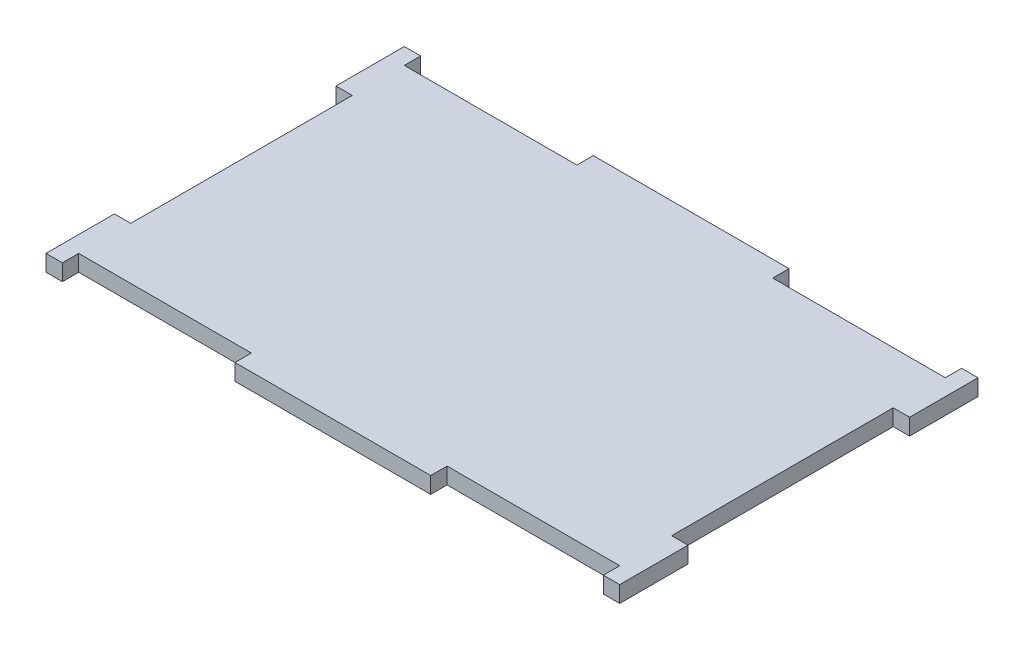
SolidWorks part; units mm, degrees
ref_plane "Front Plane" through (0, 0, 0) normal (0, 0, 1) x (1, 0, 0)
ref_plane "Top Plane" through (0, 0, 0) normal (0, 1, 0) x (1, 0, 0)
ref_plane "Right Plane" through (0, 0, 0) normal (1, 0, 0) x (0, 0, -1)
sketch "Sketch1" plane through (0, 0, 0) normal (0, 1, 0) x (1, 0, 0)
  line L0 (0, 34.775) -> (111.35, 34.775) construction
  line L1 (0, 0) -> (111.35, 0)
  line L2 (0, 0) -> (0, 69.55)
  line L3 (0, 69.55) -> (111.35, 69.55)
  line L4 (111.35, 0) -> (111.35, 69.55)
  line L5 (55.675, 69.55) -> (55.675, 0) construction
  line L6 (108.175, 56.275) -> (111.35, 13.275) construction
  line L7 (3.175, 13.275) -> (0, 13.275)
  line L8 (3.175, 13.275) -> (3.175, 56.275)
  line L9 (3.175, 56.275) -> (0, 56.275)
  line L10 (0, 13.275) -> (0, 56.275)
  line L11 (3.175, 13.275) -> (0, 56.275) construction
  line L12 (3.175, 56.275) -> (0, 13.275) construction
  line L13 (74.675, 66.375) -> (36.675, 66.375)
  line L14 (74.675, 66.375) -> (74.675, 69.55)
  line L15 (74.675, 69.55) -> (36.675, 69.55)
  line L16 (36.675, 66.375) -> (36.675, 69.55)
  line L17 (74.675, 66.375) -> (36.675, 69.55) construction
  line L18 (74.675, 69.55) -> (36.675, 66.375) construction
  line L19 (3.175, 66.375) -> (36.675, 66.375)
  line L20 (3.175, 66.375) -> (3.175, 69.55)
  line L21 (3.175, 69.55) -> (36.675, 69.55)
  line L22 (36.675, 66.375) -> (36.675, 69.55)
  line L23 (3.175, 66.375) -> (36.675, 69.55) construction
  line L24 (3.175, 69.55) -> (36.675, 66.375) construction
  line L25 (108.175, 66.375) -> (74.675, 66.375)
  line L26 (108.175, 66.375) -> (108.175, 69.55)
  line L27 (108.175, 69.55) -> (74.675, 69.55)
  line L28 (74.675, 66.375) -> (74.675, 69.55)
  line L29 (108.175, 66.375) -> (74.675, 69.55) construction
  line L30 (108.175, 69.55) -> (74.675, 66.375) construction
  line L31 (108.175, 13.275) -> (111.35, 56.275) construction
  line L32 (111.35, 13.275) -> (111.35, 56.275)
  line L33 (108.175, 56.275) -> (111.35, 56.275)
  line L34 (108.175, 13.275) -> (108.175, 56.275)
  line L35 (108.175, 13.275) -> (111.35, 13.275)
  line L36 (108.175, 0) -> (74.675, 3.175) construction
  line L37 (108.175, 3.175) -> (74.675, 0) construction
  line L38 (3.175, 0) -> (36.675, 3.175) construction
  line L39 (3.175, 3.175) -> (36.675, 0) construction
  line L40 (74.675, 0) -> (36.675, 3.175) construction
  line L41 (74.675, 3.175) -> (36.675, 0) construction
  line L42 (74.675, 3.175) -> (74.675, 0)
  line L43 (108.175, 0) -> (74.675, 0)
  line L44 (108.175, 3.175) -> (108.175, 0)
  line L45 (108.175, 3.175) -> (74.675, 3.175)
  line L46 (36.675, 3.175) -> (36.675, 0)
  line L47 (3.175, 0) -> (36.675, 0)
  line L48 (3.175, 3.175) -> (3.175, 0)
  line L49 (3.175, 3.175) -> (36.675, 3.175)
  line L50 (36.675, 3.175) -> (36.675, 0)
  line L51 (74.675, 0) -> (36.675, 0)
  line L52 (74.675, 3.175) -> (74.675, 0)
  line L53 (74.675, 3.175) -> (36.675, 3.175)
  point P9 (1.5875, 34.775)
  point P14 (55.675, 67.9625)
  point P19 (19.925, 67.9625)
  point P20 (91.425, 67.9625)
  point P29 (109.7625, 34.775)
  point P38 (91.425, 1.5875)
  point P39 (19.925, 1.5875)
  point P40 (55.675, 1.5875)
  dimension "D1" = 111.35
  dimension "D2" = 69.55
  dimension "D3" = 3.175
  dimension "D4" = 43
  dimension "D5" = 38
  dimension "D6" = 33.5
extrude "Boss-Extrude1" add sketch "Sketch1" along normal blind 3.175 contours L53 L45 L44 L1 L4 L35 L34 L33 L3 L26 L25 L13 L19 L20 L2 L9 L8 L7 L48 L49 | L16 L13 L14 L3 | L42 L53 L46 L1
